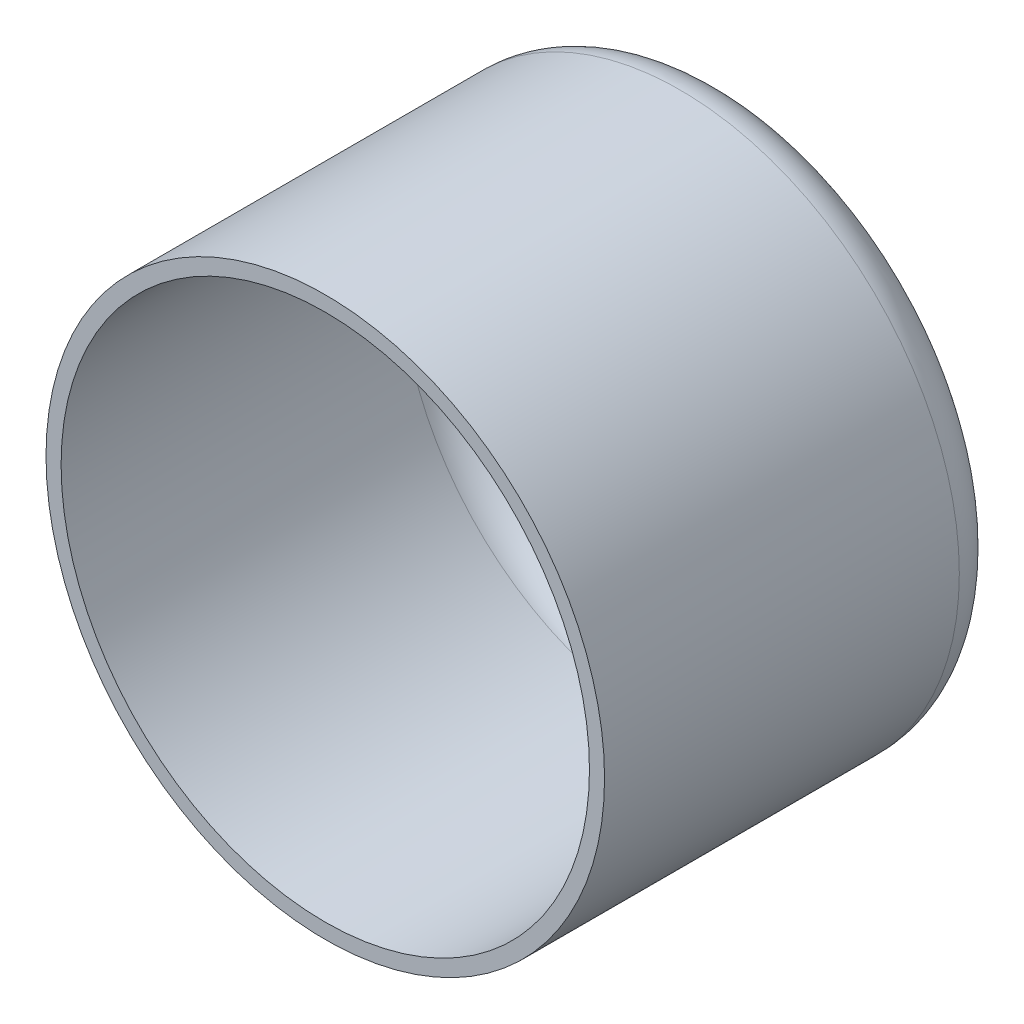
SolidWorks part; units mm, degrees
ref_plane "Front Plane" through (0, 0, 0) normal (0, 0, 1) x (1, 0, 0)
ref_plane "Top Plane" through (0, 0, 0) normal (0, 1, 0) x (1, 0, 0)
ref_plane "Right Plane" through (0, 0, 0) normal (1, 0, 0) x (0, 0, -1)
sketch "Sketch1" plane through (0, 0, 0) normal (0, 0, 1) x (1, 0, 0)
  circle A0 centre (0, 0) radius 18.5
  circle A1 centre (0.3381, -7.1921) radius 6
  dimension "D1" = 37
  dimension "D2" = 12
extrude "Extrude1" add sketch "Sketch1" along normal blind 1
sketch "Sketch2" plane through (0, 0, 1) normal (0, 0, 1) x (1, 0, 0)
  circle A0 centre (0, 0) radius 18.5 construction
  circle A1 centre (0, 0) radius 18.5
  circle A2 centre (0, 0) radius 17.5
  dimension "D1" = 1
extrude "Extrude2" add sketch "Sketch2" along normal blind 25.5
fillet "Fillet1" radius 3 2 edges at (18.5, 0, 0) (17.5, 0, 1)
